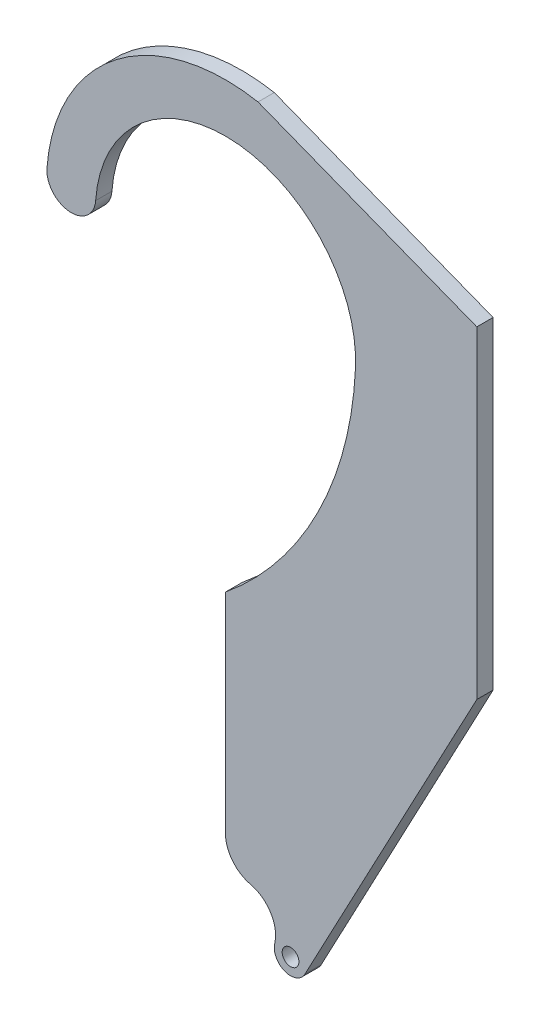
SolidWorks part; units mm, degrees
ref_plane "Front Plane" through (0, 0, 0) normal (0, 0, 1) x (1, 0, 0)
ref_plane "Top Plane" through (0, 0, 0) normal (0, 1, 0) x (1, 0, 0)
ref_plane "Right Plane" through (0, 0, 0) normal (1, 0, 0) x (0, 0, -1)
sketch "Sketch1" plane through (0, 0, 0) normal (0, 0, 1) x (1, 0, 0)
  line L0 (49.0487, 17.6816) -> (6.3525, 34.3424)
  line L1 (15.5043, -108.4828) -> (49.0487, -45.3013)
  line L3 (49.0487, 17.6816) -> (49.0487, -45.3013)
  line L4 (0, -106.9939) -> (25.4, -106.9939) construction
  line L5 (0, -92.4442) -> (0, -51.6678)
  arc A0 (25.3725, -1.1825) -> (-25.3346, 1.8216) centre (0, 0) ccw
  circle A1 centre (6.35, -92.4442) radius 6.35
  circle A2 centre (6.35, -92.4442) radius 15.875 construction
  circle A3 centre (12.7, -106.9939) radius 3.175
  arc A4 (9.6101, -106.2639) -> (4.8901, -98.6241) centre (3.4302, -104.804) ccw
  arc A5 (-34.8351, 2.5047) -> (-25.3346, 1.8216) centre (-30.0848, 2.1632) ccw
  arc A6 (6.3525, 34.3424) -> (-34.8351, 2.5047) centre (0, 0) ccw
  arc A7 (0, -51.6678) -> (25.3725, -1.1825) centre (-43.9715, 2.0493) ccw
  point P24 (12.7, -106.9939)
  dimension "D1" = 50.8
  dimension "D2" = 12.7
  dimension "D3" = 31.75
  dimension "D4" = 6.35
  dimension "D5" = 6.35
  dimension "D6" = 9.525
extrude "Boss-Extrude1" add sketch "Sketch1" along normal mid plane 3.175
hole_wizard "#4 Clearance Hole1" positions "Sketch2" profile "Sketch3" hole size "#4" standard "ANSI Inch" end condition through all
sketch "Sketch2" plane through (0, 0, 1.5875) normal (0, 0, 1) x (1, 0, 0)
  point P0 (12.7, -106.9939)
  point P3 (12.7, -106.9939)
sketch "Sketch3" plane through (12.7, -106.9939, 1.5875) normal (1, 0, 0) x (0, -1, 0)
  line L0 (0, 0) -> (0, 3.175)
  line L1 (0, 3.175) -> (1.6319, 3.175)
  line L2 (1.6319, 3.175) -> (1.6319, 0)
  line L5 (1.6319, 0) -> (0, 0)
  line L11 (0, -6.35) -> (0, 107.95) construction
  dimension "Thru Hole Dia." = 3.2639
  dimension "Thru Hole Depth" = 3.175
